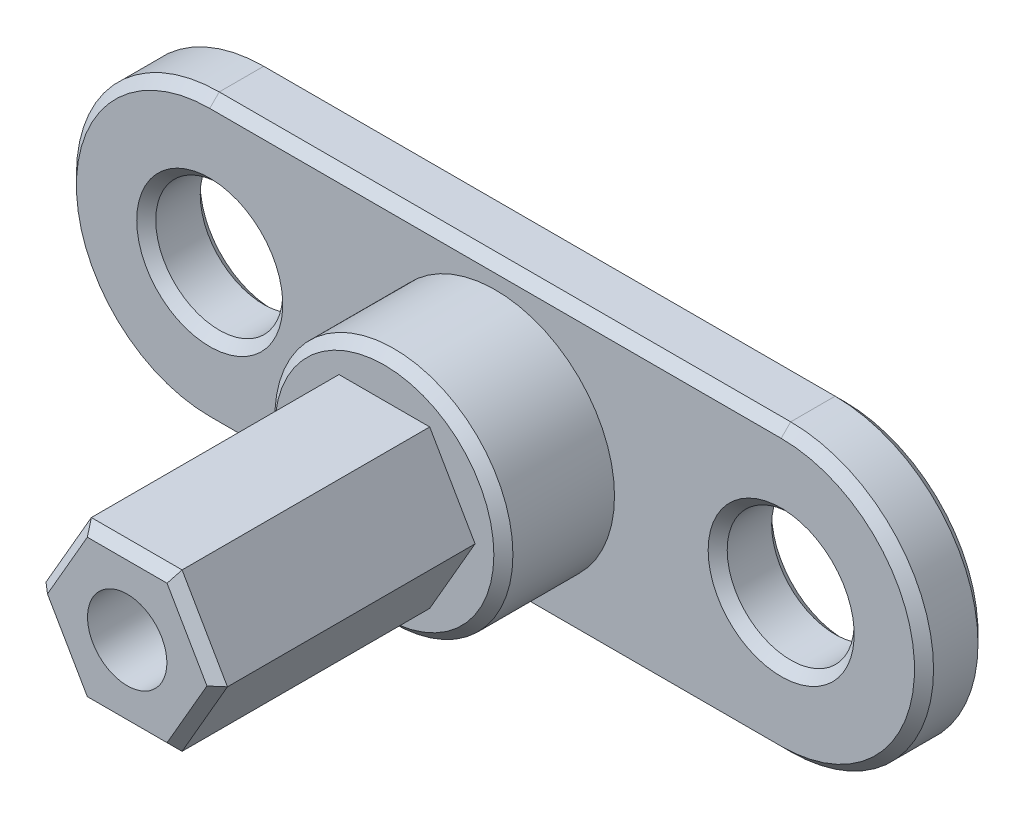
SolidWorks part; units mm, degrees
ref_plane "Front Plane" through (0, 0, 0) normal (0, 0, 1) x (1, 0, 0)
ref_plane "Top Plane" through (0, 0, 0) normal (0, 1, 0) x (1, 0, 0)
ref_plane "Right Plane" through (0, 0, 0) normal (1, 0, 0) x (0, 0, -1)
sketch "Sketch1" plane through (0, 0, 0) normal (0, 0, 1) x (1, 0, 0)
  line L1 (2.8579, -4.95) -> (5.7158, 0)
  line L2 (5.7158, 0) -> (2.8579, 4.95)
  line L3 (2.8579, 4.95) -> (-2.8579, 4.95)
  line L4 (-2.8579, 4.95) -> (-5.7158, 0)
  line L5 (-5.7158, 0) -> (-2.8579, -4.95)
  line L6 (-2.8579, -4.95) -> (2.8579, -4.95)
  circle A0 centre (0, 0) radius 4.95 construction
  dimension "D1" = 9.9
extrude "Boss-Extrude1" add sketch "Sketch1" along normal blind 16.2
sketch "Sketch2" plane through (0, 0, 0) normal (0, 0, 1) x (1, 0, 0)
  circle A0 centre (0, 0) radius 7.5
  dimension "D1" = 15
extrude "Boss-Extrude2" add sketch "Sketch2" against normal blind 7
sketch "Sketch3" plane through (0, 0, -7) normal (0, 0, -1) x (-1, 0, 0)
  line L0 (-18, 0) -> (18, 0) construction
  line L1 (-18, 9) -> (18, 9)
  line L2 (-18, -9) -> (18, -9)
  arc A0 (-18, 9) -> (-18, -9) centre (-18, 0) ccw
  arc A1 (18, -9) -> (18, 9) centre (18, 0) ccw
  circle A2 centre (-18, 0) radius 4
  circle A3 centre (18, 0) radius 4
  point P2 (0, 0)
  dimension "D3" = 8
  dimension "D1" = 18
  dimension "D2" = 36
extrude "Boss-Extrude3" add sketch "Sketch3" along normal blind 4
chamfer "Chamfer1" distance 0.6 angle 45 19 edges at (-4.2868, -2.475, 16.2) (-4.2868, 2.475, 16.2) (0, 4.95, 16.2) (4.2868, 2.475, 16.2) (4.2868, -2.475, 16.2) (0, -4.95, 16.2) (7.5, 0, 0) (14, 0, -7) (14, 0, -11) (-22, 0, -11) (-22, 0, -7) (27, 0, -11) (0, -9, -11) (0, 9, -11) (-27, 0, -11) (0, 9, -7) (27, 0, -7) (-27, 0, -7) (0, -9, -7)
sketch "Sketch4" plane through (0, 0, 16.2) normal (0, 0, 1) x (1, 0, 0)
  circle A0 centre (0, 0) radius 2.5
  dimension "D1" = 5
extrude "Cut-Extrude1" cut sketch "Sketch4" against normal blind 20
